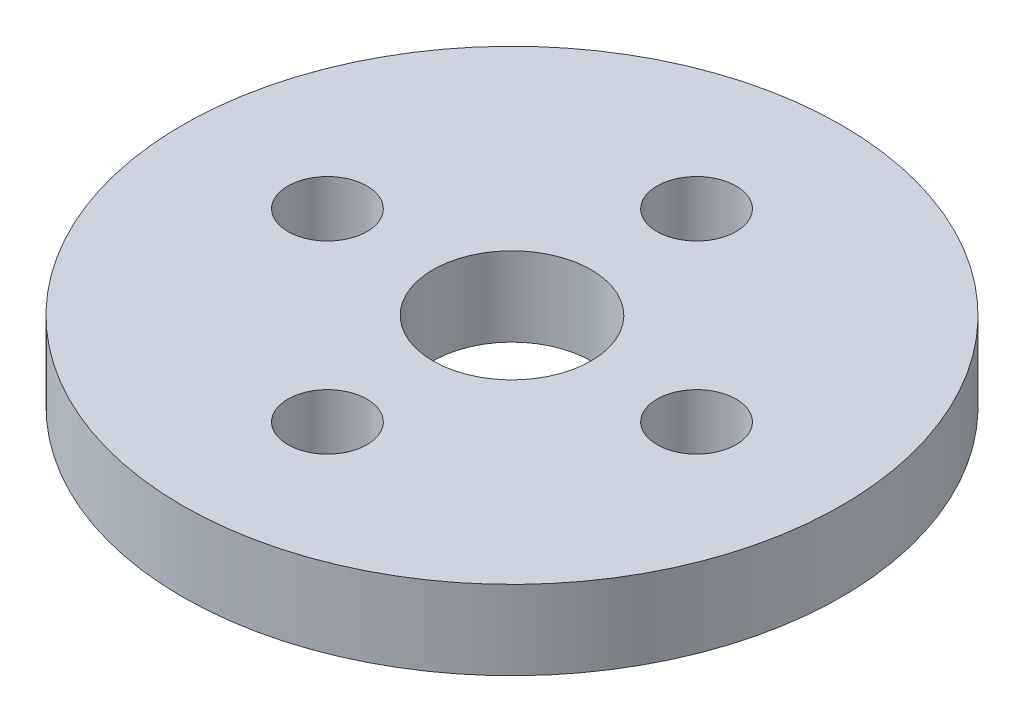
SolidWorks part; units mm, degrees
ref_plane "Front Plane" through (0, 0, 0) normal (0, 0, 1) x (1, 0, 0)
ref_plane "Top Plane" through (0, 0, 0) normal (0, 1, 0) x (1, 0, 0)
ref_plane "Right Plane" through (0, 0, 0) normal (1, 0, 0) x (0, 0, -1)
sketch "Sketch1" plane through (0, 0, 0) normal (0, 1, 0) x (1, 0, 0)
  line L0 (0, 0) -> (-7, 0) construction
  circle A0 centre (0, 0) radius 12.5
  circle A1 centre (0, 0) radius 7 construction
  circle A2 centre (-7, 0) radius 1.5
  circle A3 centre (0, 7) radius 1.5
  circle A4 centre (7, 0) radius 1.5
  circle A5 centre (0, -7) radius 1.5
  circle A6 centre (0, 0) radius 3
  point P7 (0.8289, 0)
  dimension "D1" = 25
  dimension "D2" = 14
  dimension "D3" = 3
  dimension "D6" = 6
  dimension "D4" = 4
extrude "Boss-Extrude1" add sketch "Sketch1" along normal blind 3
